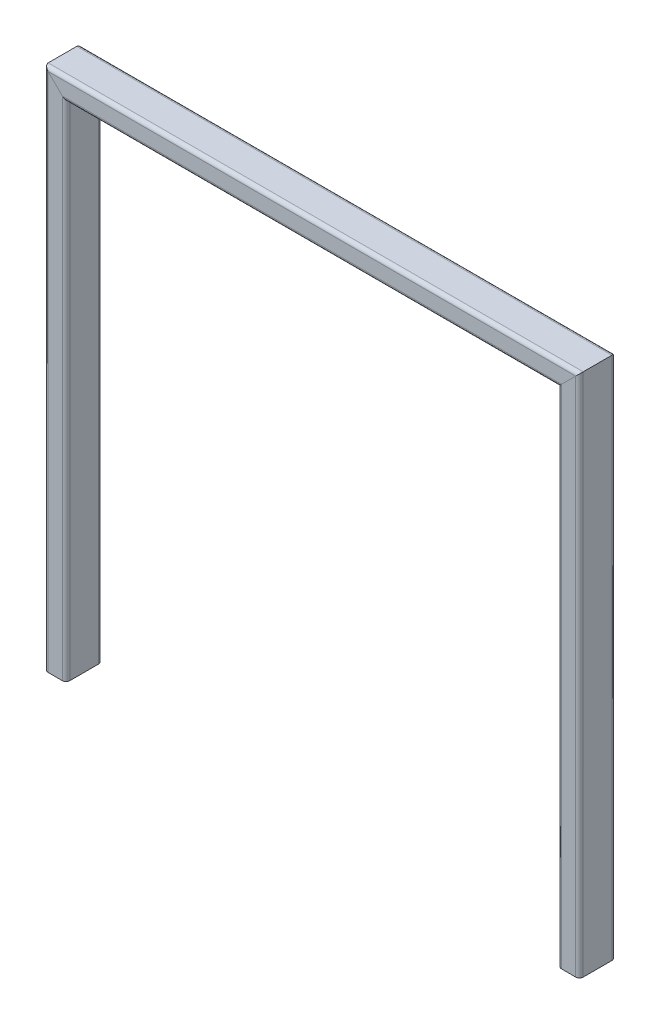
SolidWorks part; units mm, degrees
ref_plane "Front Plane" through (0, 0, 0) normal (0, 0, 1) x (1, 0, 0)
ref_plane "Top Plane" through (0, 0, 0) normal (0, 1, 0) x (1, 0, 0)
ref_plane "Right Plane" through (0, 0, 0) normal (1, 0, 0) x (0, 0, -1)
sketch3d "3DSketch1"
  line L0 (0, 0, 0) -> (0, 711.2, 0)
  line L1 (0, 711.2, 0) -> (711.2, 711.2, 0)
  line L2 (711.2, 711.2, 0) -> (711.2, 0, 0)
  dimension "D1" = 711.2
  dimension "D2" = 711.2
  dimension "D3" = 711.2
other "Rectangular tube 50 X 30 X 2.6(1)"
ref_plane "Plane1" through (0, 0, 0) normal (0, 1, 0) x (1, 0, 0)
sketch "Sketch11" plane through (0, 0, 0) normal (0, 1, 0) x (1, 0, 0)
  line L0 (-9.8, -22.4) -> (9.8, -22.4)
  line L1 (-12.4, -19.8) -> (-12.4, 19.8)
  line L2 (9.8, 22.4) -> (-9.8, 22.4)
  line L3 (12.4, 19.8) -> (12.4, -19.8)
  line L4 (-9.8, -25) -> (9.8, -25)
  line L5 (-15, -19.8) -> (-15, 19.8)
  line L6 (9.8, 25) -> (-9.8, 25)
  line L7 (15, 19.8) -> (15, -19.8)
  arc A0 (15, 19.8) -> (9.8, 25) centre (9.8, 19.8) ccw
  arc A1 (9.8, -25) -> (15, -19.8) centre (9.8, -19.8) ccw
  arc A2 (-15, -19.8) -> (-9.8, -25) centre (-9.8, -19.8) ccw
  arc A3 (-9.8, 25) -> (-15, 19.8) centre (-9.8, 19.8) ccw
  arc A4 (-9.8, 22.4) -> (-12.4, 19.8) centre (-9.8, 19.8) ccw
  arc A5 (12.4, 19.8) -> (9.8, 22.4) centre (9.8, 19.8) ccw
  arc A6 (9.8, -22.4) -> (12.4, -19.8) centre (9.8, -19.8) ccw
  arc A7 (-12.4, -19.8) -> (-9.8, -22.4) centre (-9.8, -19.8) ccw
  point P0 (0, 25)
  point P1 (15, 0)
  point P2 (0, -25)
  point P3 (-15, 0)
  point P4 (-15, 25)
  point P5 (15, 25)
  point P6 (15, -25)
  point P7 (-15, -25)
  point P8 (0, 0)
  point P33 (0, 0)
  dimension "D1" = 5.2
  dimension "Thickness" = 2.6
  dimension "V_leg" = 50
  dimension "H_leg" = 30
